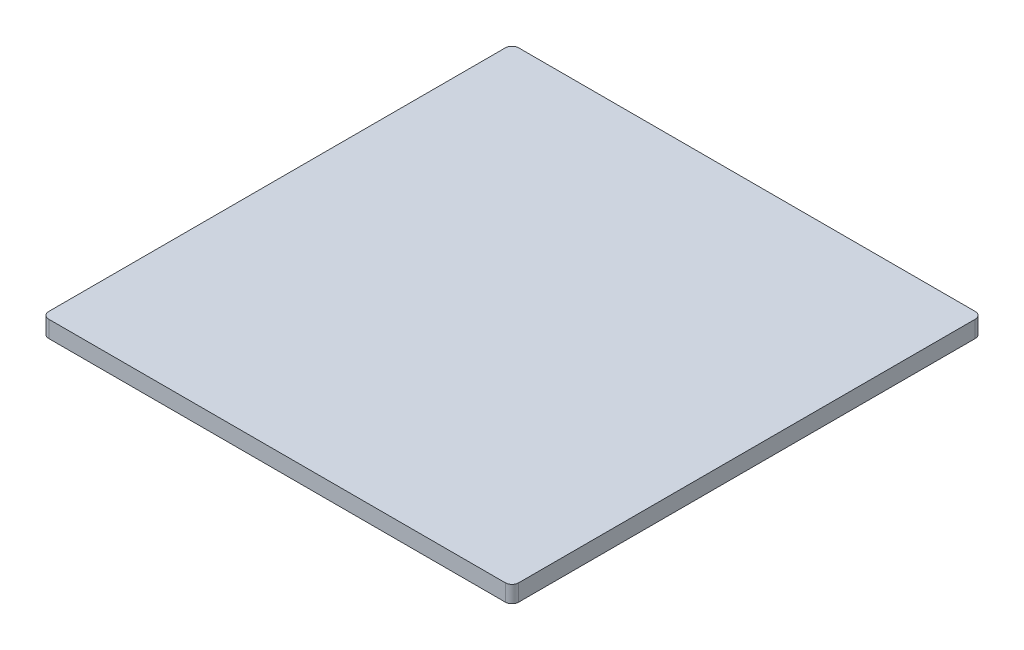
SolidWorks part; units mm, degrees
ref_plane "Front Plane" through (0, 0, 0) normal (0, 0, 1) x (1, 0, 0)
ref_plane "Top Plane" through (0, 0, 0) normal (0, 1, 0) x (1, 0, 0)
ref_plane "Right Plane" through (0, 0, 0) normal (1, 0, 0) x (0, 0, -1)
sketch "Sketch2" plane through (0, 0, 0) normal (0, 1, 0) x (1, 0, 0)
  line L1 (-86.36, -88.9) -> (86.36, -88.9)
  line L2 (-88.9, -86.36) -> (-88.9, 86.36)
  line L3 (-86.36, 88.9) -> (86.36, 88.9)
  line L4 (88.9, -86.36) -> (88.9, 86.36)
  line L5 (-88.9, -88.9) -> (88.9, 88.9) construction
  line L6 (-88.9, 88.9) -> (88.9, -88.9) construction
  arc A0 (-86.36, -88.9) -> (-88.9, -86.36) centre (-86.36, -86.36) cw
  arc A1 (86.36, -88.9) -> (88.9, -86.36) centre (86.36, -86.36) ccw
  arc A2 (86.36, 88.9) -> (88.9, 86.36) centre (86.36, 86.36) cw
  arc A3 (-88.9, 86.36) -> (-86.36, 88.9) centre (-86.36, 86.36) cw
  point P0 (0, 0)
  dimension "D3" = 2.54
  dimension "D1" = 177.8
  dimension "D2" = 177.8
extrude "Boss-Extrude1" add sketch "Sketch2" along normal blind 6.35
